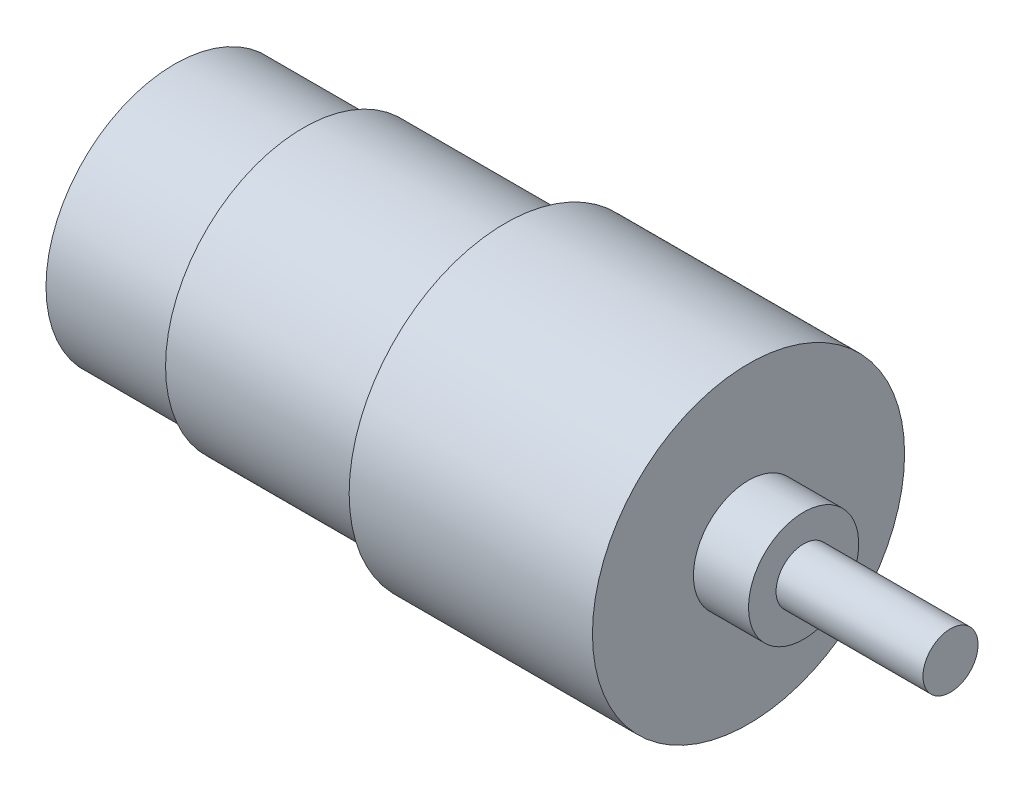
SolidWorks part; units mm, degrees
ref_plane "Front Plane" through (0, 0, 0) normal (0, 0, 1) x (1, 0, 0)
ref_plane "Top Plane" through (0, 0, 0) normal (0, 1, 0) x (1, 0, 0)
ref_plane "Right Plane" through (0, 0, 0) normal (1, 0, 0) x (0, 0, -1)
sketch "Sketch1" plane through (0, 0, 0) normal (0, 1, 0) x (1, 0, 0)
  line L0 (-18.6529, 0) -> (84.5194, 0) construction
  line L1 (0, 0) -> (0, 14)
  line L2 (0, 14) -> (14.0218, 14)
  line L3 (14.0218, 14) -> (14.0218, 15)
  line L4 (14.0218, 15) -> (36.0194, 15)
  line L5 (36.0194, 15) -> (36.0194, 17)
  line L6 (36.0194, 17) -> (62.5194, 17)
  line L7 (62.5194, 17) -> (62.5194, 6)
  line L8 (62.5194, 6) -> (68.5194, 6)
  line L9 (68.5194, 6) -> (68.5194, 3)
  line L10 (68.5194, 3) -> (84.5194, 3)
  line L11 (84.5194, 3) -> (84.5194, 0)
  line L12 (84.5194, 0) -> (0, 0)
  dimension "D1" = 26.5
  dimension "D2" = 6
  dimension "D3" = 22
  dimension "D4" = 6
  dimension "D5" = 12
  dimension "D6" = 34
  dimension "D7" = 30
  dimension "D8" = 28
revolve "Revolve1" add sketch "Sketch1" angle 360 about L0
